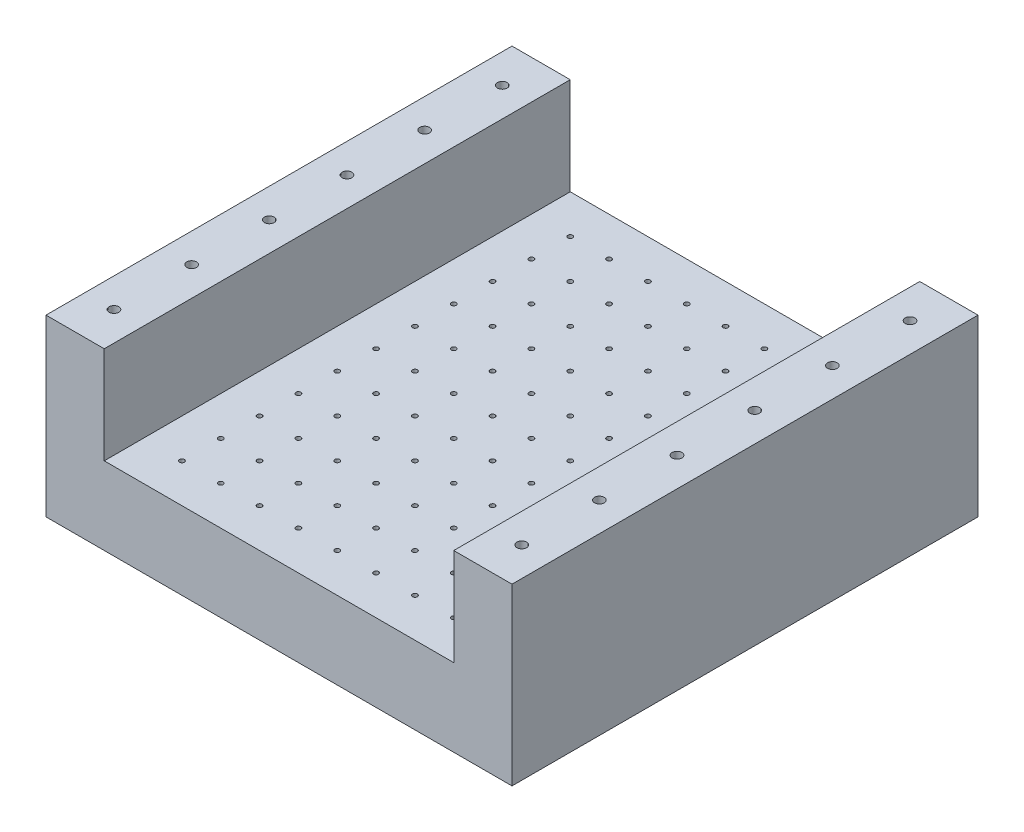
SolidWorks part; units mm, degrees
ref_plane "Front Plane" through (0, 0, 0) normal (0, 0, 1) x (1, 0, 0)
ref_plane "Top Plane" through (0, 0, 0) normal (0, 1, 0) x (1, 0, 0)
ref_plane "Right Plane" through (0, 0, 0) normal (1, 0, 0) x (0, 0, -1)
sketch "Sketch2" plane through (0, 0, 0) normal (0, 1, 0) x (1, 0, 0)
  line L1 (104.0534, 37.3747) -> (713.6534, 37.3747)
  line L2 (104.0534, 37.3747) -> (104.0534, -572.2253)
  line L3 (104.0534, -572.2253) -> (713.6534, -572.2253)
  line L4 (713.6534, 37.3747) -> (713.6534, -572.2253)
  dimension "D1" = 609.6
  dimension "D2" = 609.6
extrude "Boss-Extrude1" add sketch "Sketch2" along normal blind 101.6
sketch "Sketch4" plane through (0, 101.6, 0) normal (0, 1, 0) x (1, 0, 0)
  line L0 (104.0534, -572.2253) -> (713.6534, -572.2253) construction
  line L1 (104.0534, 37.3747) -> (180.2534, 37.3747)
  line L2 (104.0534, 37.3747) -> (104.0534, -572.2253)
  line L3 (104.0534, -572.2253) -> (180.2534, -572.2253)
  line L4 (180.2534, 37.3747) -> (180.2534, -572.2253)
  line L6 (713.6534, 37.3747) -> (637.4534, 37.3747)
  line L7 (713.6534, 37.3747) -> (713.6534, -572.2253)
  line L8 (713.6534, -572.2253) -> (637.4534, -572.2253)
  line L9 (637.4534, 37.3747) -> (637.4534, -572.2253)
  dimension "D1" = 76.2
  dimension "D2" = 76.2
extrude "Boss-Extrude2" add sketch "Sketch4" along normal blind 127
sketch "Sketch5" plane through (0, 228.6, 0) normal (0, 1, 0) x (1, 0, 0)
  line L0 (180.2534, 37.3747) -> (104.0534, 37.3747) construction
  line L1 (142.1534, -13.4253) -> (142.1534, -115.0253) construction
  line L2 (104.0534, 37.3747) -> (104.0534, -572.2253) construction
  circle A0 centre (142.1534, -13.4253) radius 6.35
  circle A1 centre (142.1534, -115.0253) radius 6.35
  circle A2 centre (142.1534, -216.6253) radius 6.35
  circle A3 centre (142.1534, -318.2253) radius 6.35
  circle A4 centre (142.1534, -419.8253) radius 6.35
  circle A5 centre (142.1534, -521.4253) radius 6.35
  dimension "D1" = 12.7
  dimension "D2" = 50.8
  dimension "D4" = 101.6
  dimension "D5" = 38.1
  dimension "D3" = 6
extrude "Cut-Extrude1" cut sketch "Sketch5" against normal blind 50.8
pattern_linear "LPattern1" count 2 spacing 533.4 along (1, 0, 0) of "Cut-Extrude1"
sketch "Sketch6" plane through (0, 101.6, 0) normal (0, 1, 0) x (1, 0, 0)
  line L0 (180.2534, -572.2253) -> (637.4534, -572.2253) construction
  line L1 (180.2534, -572.2253) -> (180.2534, 37.3747) construction
  line L2 (231.0534, -521.4253) -> (231.0534, -470.6253) construction
  circle A0 centre (231.0534, -521.4253) radius 3.175
  circle A1 centre (231.0534, -470.6253) radius 3.175
  circle A2 centre (231.0534, -419.8253) radius 3.175
  circle A3 centre (231.0534, -369.0253) radius 3.175
  circle A4 centre (231.0534, -318.2253) radius 3.175
  circle A5 centre (231.0534, -267.4253) radius 3.175
  circle A6 centre (231.0534, -216.6253) radius 3.175
  circle A7 centre (231.0534, -165.8253) radius 3.175
  circle A8 centre (231.0534, -115.0253) radius 3.175
  circle A9 centre (231.0534, -64.2253) radius 3.175
  circle A10 centre (231.0534, -13.4253) radius 3.175
  circle A11 centre (281.8534, -521.4253) radius 3.175
  circle A12 centre (281.8534, -470.6253) radius 3.175
  circle A13 centre (281.8534, -419.8253) radius 3.175
  circle A14 centre (281.8534, -369.0253) radius 3.175
  circle A15 centre (281.8534, -318.2253) radius 3.175
  circle A16 centre (281.8534, -267.4253) radius 3.175
  circle A17 centre (281.8534, -216.6253) radius 3.175
  circle A18 centre (281.8534, -165.8253) radius 3.175
  circle A19 centre (281.8534, -115.0253) radius 3.175
  circle A20 centre (281.8534, -64.2253) radius 3.175
  circle A21 centre (281.8534, -13.4253) radius 3.175
  circle A22 centre (332.6534, -521.4253) radius 3.175
  circle A23 centre (332.6534, -470.6253) radius 3.175
  circle A24 centre (332.6534, -419.8253) radius 3.175
  circle A25 centre (332.6534, -369.0253) radius 3.175
  circle A26 centre (332.6534, -318.2253) radius 3.175
  circle A27 centre (332.6534, -267.4253) radius 3.175
  circle A28 centre (332.6534, -216.6253) radius 3.175
  circle A29 centre (332.6534, -165.8253) radius 3.175
  circle A30 centre (332.6534, -115.0253) radius 3.175
  circle A31 centre (332.6534, -64.2253) radius 3.175
  circle A32 centre (332.6534, -13.4253) radius 3.175
  circle A33 centre (383.4534, -521.4253) radius 3.175
  circle A34 centre (383.4534, -470.6253) radius 3.175
  circle A35 centre (383.4534, -419.8253) radius 3.175
  circle A36 centre (383.4534, -369.0253) radius 3.175
  circle A37 centre (383.4534, -318.2253) radius 3.175
  circle A38 centre (383.4534, -267.4253) radius 3.175
  circle A39 centre (383.4534, -216.6253) radius 3.175
  circle A40 centre (383.4534, -165.8253) radius 3.175
  circle A41 centre (383.4534, -115.0253) radius 3.175
  circle A42 centre (383.4534, -64.2253) radius 3.175
  circle A43 centre (383.4534, -13.4253) radius 3.175
  circle A44 centre (434.2534, -521.4253) radius 3.175
  circle A45 centre (434.2534, -470.6253) radius 3.175
  circle A46 centre (434.2534, -419.8253) radius 3.175
  circle A47 centre (434.2534, -369.0253) radius 3.175
  circle A48 centre (434.2534, -318.2253) radius 3.175
  circle A49 centre (434.2534, -267.4253) radius 3.175
  circle A50 centre (434.2534, -216.6253) radius 3.175
  circle A51 centre (434.2534, -165.8253) radius 3.175
  circle A52 centre (434.2534, -115.0253) radius 3.175
  circle A53 centre (434.2534, -64.2253) radius 3.175
  circle A54 centre (434.2534, -13.4253) radius 3.175
  circle A55 centre (485.0534, -521.4253) radius 3.175
  circle A56 centre (485.0534, -470.6253) radius 3.175
  circle A57 centre (485.0534, -419.8253) radius 3.175
  circle A58 centre (485.0534, -369.0253) radius 3.175
  circle A59 centre (485.0534, -318.2253) radius 3.175
  circle A60 centre (485.0534, -267.4253) radius 3.175
  circle A61 centre (485.0534, -216.6253) radius 3.175
  circle A62 centre (485.0534, -165.8253) radius 3.175
  circle A63 centre (485.0534, -115.0253) radius 3.175
  circle A64 centre (485.0534, -64.2253) radius 3.175
  circle A65 centre (485.0534, -13.4253) radius 3.175
  circle A66 centre (535.8534, -521.4253) radius 3.175
  circle A67 centre (535.8534, -470.6253) radius 3.175
  circle A68 centre (535.8534, -419.8253) radius 3.175
  circle A69 centre (535.8534, -369.0253) radius 3.175
  circle A70 centre (535.8534, -318.2253) radius 3.175
  circle A71 centre (535.8534, -267.4253) radius 3.175
  circle A72 centre (535.8534, -216.6253) radius 3.175
  circle A73 centre (535.8534, -165.8253) radius 3.175
  circle A74 centre (535.8534, -115.0253) radius 3.175
  circle A75 centre (535.8534, -64.2253) radius 3.175
  circle A76 centre (535.8534, -13.4253) radius 3.175
  circle A77 centre (586.6534, -521.4253) radius 3.175
  circle A78 centre (586.6534, -470.6253) radius 3.175
  circle A79 centre (586.6534, -419.8253) radius 3.175
  circle A80 centre (586.6534, -369.0253) radius 3.175
  circle A81 centre (586.6534, -318.2253) radius 3.175
  circle A82 centre (586.6534, -267.4253) radius 3.175
  circle A83 centre (586.6534, -216.6253) radius 3.175
  circle A84 centre (586.6534, -165.8253) radius 3.175
  circle A85 centre (586.6534, -115.0253) radius 3.175
  circle A86 centre (586.6534, -64.2253) radius 3.175
  circle A87 centre (586.6534, -13.4253) radius 3.175
  dimension "D1" = 6.35
  dimension "D2" = 50.8
  dimension "D3" = 50.8
  dimension "D6" = 50.8
  dimension "D4" = 11
  dimension "D5" = 8
extrude "Cut-Extrude2" cut sketch "Sketch6" against normal blind 50.8
